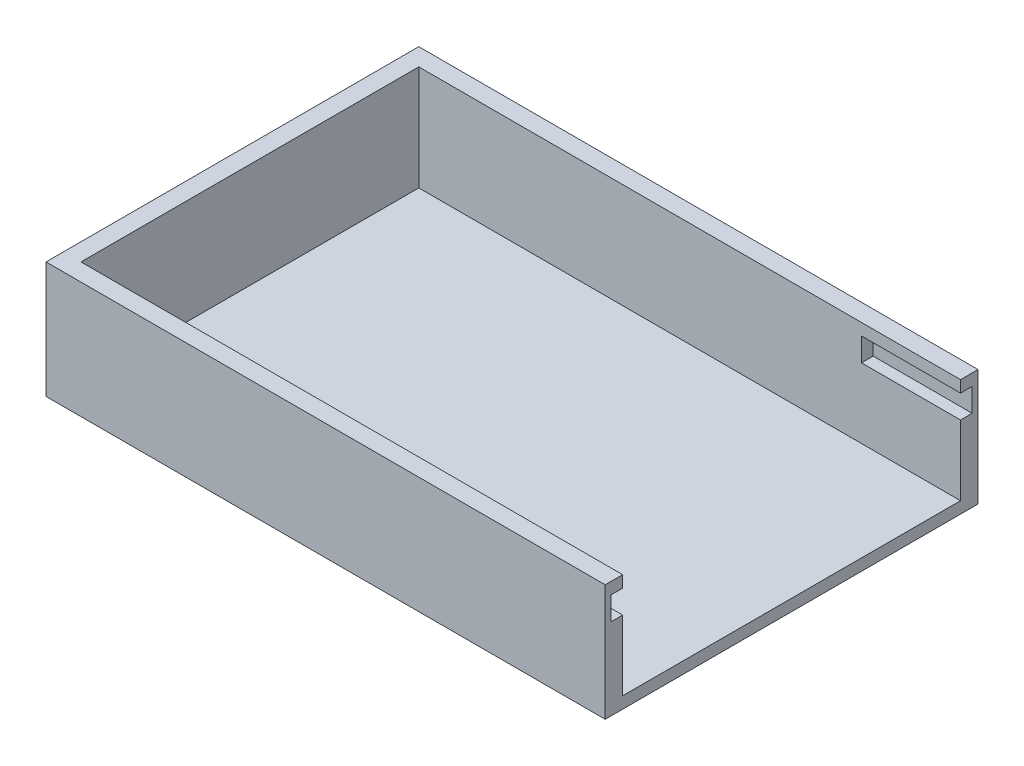
SolidWorks part; units mm, degrees
ref_plane "Front Plane" through (0, 0, 0) normal (0, 0, 1) x (1, 0, 0)
ref_plane "Top Plane" through (0, 0, 0) normal (0, 1, 0) x (1, 0, 0)
ref_plane "Right Plane" through (0, 0, 0) normal (1, 0, 0) x (0, 0, -1)
sketch "Sketch1" plane through (0, 0, 0) normal (0, 1, 0) x (1, 0, 0)
  line L1 (76.2, -50.8) -> (-76.2, -50.8)
  line L2 (76.2, -50.8) -> (76.2, 50.8)
  line L3 (76.2, 50.8) -> (-76.2, 50.8)
  line L4 (-76.2, -50.8) -> (-76.2, 50.8)
  line L5 (76.2, -50.8) -> (-76.2, 50.8) construction
  line L6 (76.2, 50.8) -> (-76.2, -50.8) construction
  point P0 (0, 0)
  dimension "D1" = 101.6
  dimension "D2" = 152.4
extrude "Boss-Extrude1" add sketch "Sketch1" along normal blind 31.75
sketch "Sketch2" plane through (0, 31.75, 0) normal (0, 1, 0) x (1, 0, 0)
  line L0 (-76.2, 50.8) -> (-76.2, -50.8) construction
  line L1 (71.4375, -46.0375) -> (-71.4375, -46.0375)
  line L3 (71.4375, 46.0375) -> (-71.4375, 46.0375)
  line L4 (-71.4375, -46.0375) -> (-71.4375, 46.0375)
  line L5 (71.4375, -46.0375) -> (-71.4375, 46.0375) construction
  line L6 (71.4375, 46.0375) -> (-71.4375, -46.0375) construction
  line L7 (76.2, 50.8) -> (-76.2, 50.8) construction
  line L8 (71.4375, 46.0375) -> (80.9625, 46.0375)
  line L9 (80.9625, 46.0375) -> (80.9625, -46.0375)
  line L10 (80.9625, -46.0375) -> (71.4375, -46.0375)
  line L11 (-76.2, -50.8) -> (76.2, -50.8) construction
  line L12 (76.2, -50.8) -> (76.2, 50.8) construction
  point P0 (0, 0)
  dimension "D1" = 4.7625
  dimension "D2" = 4.7625
  dimension "D3" = 4.7625
  dimension "D4" = 4.7625
extrude "Cut-Extrude1" cut sketch "Sketch2" against normal offset from surface (28.575 mm away) 3.175 up to face at (0, 0, 0)
sketch "Sketch3" plane through (76.2, 0, 0) normal (1, 0, 0) x (0, 0, -1)
  line L0 (-44.45, 22.225) -> (-44.45, 28.575)
  line L1 (-44.45, 28.575) -> (-49.2125, 28.575)
  line L2 (-49.2125, 28.575) -> (-49.2125, 22.225)
  line L3 (-49.2125, 22.225) -> (-44.45, 22.225)
  line L4 (44.45, 28.575) -> (44.45, 22.225)
  line L5 (44.45, 22.225) -> (49.2125, 22.225)
  line L6 (49.2125, 22.225) -> (49.2125, 28.575)
  line L7 (49.2125, 28.575) -> (44.45, 28.575)
  line L12 (-46.0375, 23.8125) -> (-46.0375, 26.9875)
  line L13 (-46.0375, 26.9875) -> (-47.625, 26.9875)
  line L14 (-47.625, 26.9875) -> (-47.625, 23.8125)
  line L15 (-47.625, 23.8125) -> (-46.0375, 23.8125)
  line L16 (-46.0375, 23.8125) -> (-46.0375, 26.9875) construction
  line L17 (-46.0375, 26.9875) -> (-47.625, 26.9875) construction
  line L18 (-47.625, 26.9875) -> (-47.625, 23.8125) construction
  line L19 (-47.625, 23.8125) -> (-46.0375, 23.8125) construction
  line L20 (46.0375, 26.9875) -> (46.0375, 23.8125)
  line L21 (47.625, 26.9875) -> (46.0375, 26.9875)
  line L22 (47.625, 23.8125) -> (47.625, 26.9875)
  line L23 (46.0375, 23.8125) -> (47.625, 23.8125)
  line L24 (46.0375, 26.9875) -> (46.0375, 23.8125) construction
  line L25 (47.625, 26.9875) -> (46.0375, 26.9875) construction
  line L26 (47.625, 23.8125) -> (47.625, 26.9875) construction
  line L27 (46.0375, 23.8125) -> (47.625, 23.8125) construction
  dimension "D1" = 1.5875
  dimension "D2" = 0
  dimension "D3" = 0
extrude "Cut-Extrude2" cut sketch "Sketch3" against normal blind 26.9875
